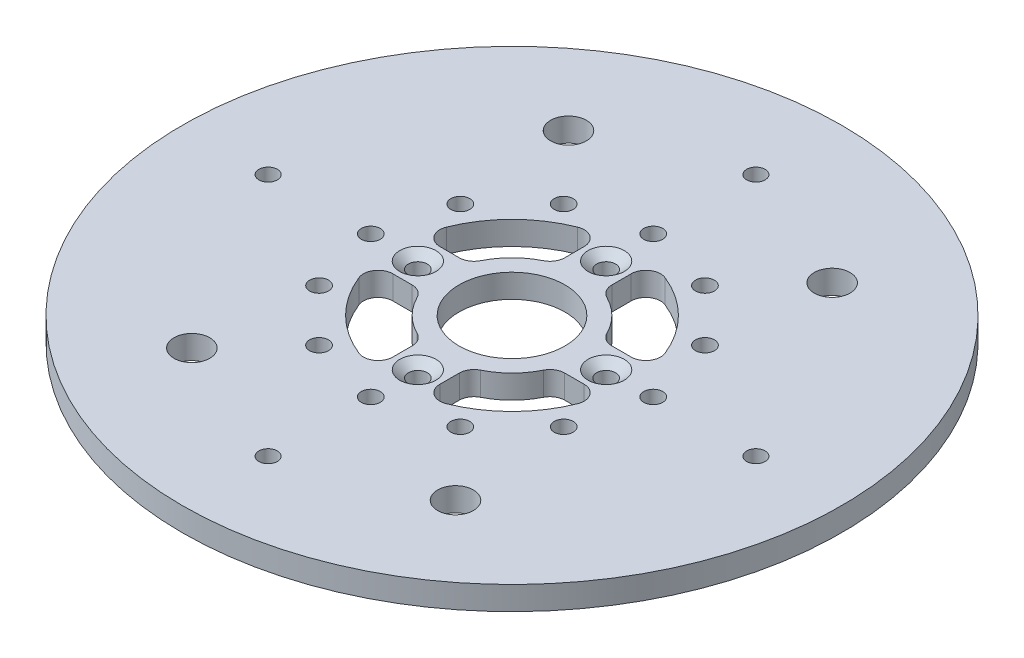
SolidWorks part; units mm, degrees
material "6061-T6 (SS)"
ref_plane "Front Plane" through (0, 0, 0) normal (0, 0, 1) x (1, 0, 0)
ref_plane "Top Plane" through (0, 0, 0) normal (0, 1, 0) x (1, 0, 0)
ref_plane "Right Plane" through (0, 0, 0) normal (1, 0, 0) x (0, 0, -1)
sketch "Sketch1" plane through (0, 0, 0) normal (0, 1, 0) x (1, 0, 0)
  circle A5 centre (0, 0) radius 88.9
  point P14 (0, 0)
  dimension "D4" = 177.8
extrude "Boss-Extrude1" add sketch "Sketch1" along normal blind 6.35
sketch "Sketch2" plane through (0, 6.35, 0) normal (0, 1, 0) x (1, 0, 0)
  circle A0 centre (0, 0) radius 14.2875
  dimension "D1" = 28.575
extrude "Cut-Extrude1" cut sketch "Sketch2" against normal through all
hole_wizard "CSK for #10 Flat Head Machine Screw (100)1" positions "Sketch5" profile "Sketch6" countersink size "#10" standard "ANSI Inch" end condition through all
sketch "Sketch5" plane through (0, 6.35, 0) normal (0, 1, 0) x (1, 0, 0)
  line L0 (0, 25.4) -> (0, 0) construction
  circle A0 centre (0, 0) radius 25.4
  point P0 (0, 25.4)
  point P13 (25.4, 0)
  point P15 (0, -25.4)
  point P17 (-25.4, 0)
  dimension "D1" = 50.8
sketch "Sketch6" plane through (0, 6.35, -25.4) normal (1, 0, 0) x (0, 0, 1)
  line L0 (0, 0) -> (0, 6.35)
  line L1 (0, 6.35) -> (2.5527, 6.35)
  line L2 (2.5527, 6.35) -> (2.5527, 1.9608)
  line L3 (2.5527, 1.9608) -> (4.8895, 0)
  line L5 (4.8895, 0) -> (0, 0)
  line L6 (-2.5527, 1.9608) -> (-4.8895, 0) construction
  line L11 (0, -6.35) -> (0, 107.95) construction
  dimension "Thru Hole Dia." = 5.1054
  dimension "Thru Hole Depth" = 6.35
  dimension "Near C'Sink Dia." = 9.779
  dimension "Near C'Sink Angle" = 100
hole_wizard "#9 (0.196) Diameter Hole1" positions "Sketch11" profile "Sketch10" hole size "#9" standard "ANSI Inch" end condition through all
sketch "Sketch11" plane through (0, 6.35, 0) normal (0, 1, 0) x (1, 0, 0)
  circle A0 centre (0, 0) radius 65.786
  point P0 (0, 65.786)
  point P9 (65.786, 0)
  point P11 (0, -65.786)
  point P13 (-65.786, 0)
  dimension "D1" = 131.572
sketch "Sketch10" plane through (0, 6.35, -65.786) normal (1, 0, 0) x (0, 0, 1)
  line L0 (0, 0) -> (0, 6.35)
  line L1 (0, 6.35) -> (2.4892, 6.35)
  line L2 (2.4892, 6.35) -> (2.4892, 0)
  line L5 (2.4892, 0) -> (0, 0)
  line L11 (0, -6.35) -> (0, 107.95) construction
  dimension "Thru Hole Dia." = 4.9784
  dimension "Thru Hole Depth" = 6.35
sketch "Sketch12" plane through (0, 6.35, 0) normal (0, 1, 0) x (1, 0, 0)
  line L0 (6.35, 48.93) -> (6.35, 79.5019)
  line L1 (48.93, 6.35) -> (79.5019, 6.35)
  line L2 (6.35, -48.93) -> (6.35, -79.5019)
  line L3 (48.93, -6.35) -> (79.5019, -6.35)
  line L4 (-48.93, -6.35) -> (-79.5019, -6.35)
  line L5 (-6.35, -48.93) -> (-6.35, -79.5019)
  line L6 (-6.35, 48.93) -> (-6.35, 79.5019)
  line L7 (-48.93, 6.35) -> (-79.5019, 6.35)
  arc A0 (9.4998, 45.0467) -> (45.0467, 9.4998) centre (0, 0) cw
  circle A1 centre (65.786, 0) radius 2.4892 construction
  circle A2 centre (0, 25.4) radius 2.5527 construction
  circle A3 centre (0, 0) radius 14.2875 construction
  arc A4 (10.8296, 83.4376) -> (83.4376, 10.8296) centre (0, 0) cw
  circle A5 centre (0, 0) radius 88.9 construction
  arc A6 (79.5019, 6.35) -> (83.4376, 10.8296) centre (79.5019, 10.3187) ccw
  arc A7 (45.0467, 9.4998) -> (48.93, 6.35) centre (48.93, 10.3187) ccw
  arc A8 (6.35, 48.93) -> (9.4998, 45.0467) centre (10.3188, 48.93) ccw
  arc A9 (6.35, 79.5019) -> (10.8296, 83.4376) centre (10.3187, 79.5019) cw
  arc A10 (9.4998, -45.0467) -> (6.35, -48.93) centre (10.3188, -48.93) ccw
  arc A11 (6.35, -79.5019) -> (10.8296, -83.4376) centre (10.3188, -79.5019) ccw
  arc A12 (83.4376, -10.8296) -> (10.8296, -83.4376) centre (0, 0) cw
  arc A13 (79.5019, -6.35) -> (83.4376, -10.8296) centre (79.5019, -10.3188) cw
  arc A14 (48.93, -6.35) -> (45.0467, -9.4998) centre (48.93, -10.3188) ccw
  arc A15 (45.0467, -9.4998) -> (9.4998, -45.0467) centre (0, 0) cw
  arc A16 (-45.0467, -9.4998) -> (-48.93, -6.35) centre (-48.93, -10.3187) ccw
  arc A17 (-79.5019, -6.35) -> (-83.4376, -10.8296) centre (-79.5019, -10.3188) ccw
  arc A18 (-10.8296, -83.4376) -> (-83.4376, -10.8296) centre (0, 0) cw
  arc A19 (-6.35, -79.5019) -> (-10.8296, -83.4376) centre (-10.3187, -79.5019) cw
  arc A20 (-6.35, -48.93) -> (-9.4998, -45.0467) centre (-10.3187, -48.93) ccw
  arc A21 (-9.4998, -45.0467) -> (-45.0467, -9.4998) centre (0, 0) cw
  arc A22 (-9.4998, 45.0467) -> (-6.35, 48.93) centre (-10.3188, 48.93) ccw
  arc A23 (-6.35, 79.5019) -> (-10.8296, 83.4376) centre (-10.3188, 79.5019) ccw
  arc A24 (-83.4376, 10.8296) -> (-10.8296, 83.4376) centre (0, 0) cw
  arc A25 (-79.5019, 6.35) -> (-83.4376, 10.8296) centre (-79.5019, 10.3188) cw
  arc A26 (-48.93, 6.35) -> (-45.0467, 9.4998) centre (-48.93, 10.3188) ccw
  arc A27 (-45.0467, 9.4998) -> (-9.4998, 45.0467) centre (0, 0) cw
  point P61 (0, 0)
  dimension "D1" = 6.35
  dimension "D3" = 31.75
  dimension "D4" = 4.7625
  dimension "D5" = 3.9688
  dimension "D2" = 6.35
  dimension "D6" = 4
extrude "Cut-Extrude2" [suppressed] cut sketch "Sketch12" against normal through all
hole_wizard "1/4-20 Tapped Hole1" positions "Sketch14" profile "Sketch15" tap size "1/4-20" standard "ANSI Inch" end condition through all
sketch "Sketch14" plane through (0, 6.35, 0) normal (0, 1, 0) x (1, 0, 0)
  line L0 (0, 0) -> (0, 38.1) construction
  line L1 (0, 0) -> (38.1, 0) construction
  circle A0 centre (0, 0) radius 38.1 construction
  point P0 (0, 38.1)
  point P12 (19.05, 32.9956)
  point P13 (32.9956, 19.05)
  point P14 (38.1, 0)
  point P15 (32.9956, -19.05)
  point P16 (19.05, -32.9956)
  point P17 (0, -38.1)
  point P18 (-19.05, -32.9956)
  point P19 (-32.9956, -19.05)
  point P20 (-38.1, 0)
  point P21 (-32.9956, 19.05)
  point P22 (-19.05, 32.9956)
  dimension "D1" = 38.1
  dimension "D2" = 12
sketch "Sketch15" plane through (0, 6.35, -38.1) normal (1, 0, 0) x (0, 0, 1)
  line L0 (0, 0) -> (0, 6.35)
  line L1 (0, 6.35) -> (2.5527, 6.35)
  line L2 (2.5527, 6.35) -> (2.5527, 0)
  line L5 (2.5527, 0) -> (0, 0)
  line L11 (0, -6.35) -> (0, 107.95) construction
  dimension "Thru Tap Drill Dia." = 5.1054
  dimension "Thru Tap Drill Depth" = 6.35
cosmetic thread "Hole Thread1" parameters "D2"=6.35
cosmetic thread "Hole Thread2" parameters "D2"=6.35
cosmetic thread "Hole Thread3" parameters "D2"=6.35
cosmetic thread "Hole Thread4" parameters "D2"=6.35
cosmetic thread "Hole Thread5" parameters "D2"=6.35
cosmetic thread "Hole Thread6" parameters "D2"=6.35
cosmetic thread "Hole Thread7" parameters "D2"=6.35
cosmetic thread "Hole Thread8" parameters "D2"=6.35
cosmetic thread "Hole Thread9" parameters "D2"=6.35
cosmetic thread "Hole Thread10" parameters "D2"=6.35
cosmetic thread "Hole Thread11" parameters "D2"=6.35
cosmetic thread "Hole Thread12" parameters "D2"=6.35
sketch "Sketch16" plane through (0, 6.35, 0) normal (0, 1, 0) x (1, 0, 0)
  line L0 (20.5764, 6.35) -> (25.7938, 6.35)
  line L1 (6.35, 20.5764) -> (6.35, 25.7938)
  line L2 (6.35, -20.5764) -> (6.35, -25.7938)
  line L3 (20.5764, -6.35) -> (25.7938, -6.35)
  line L4 (-20.5764, -6.35) -> (-25.7938, -6.35)
  line L5 (-6.35, -20.5764) -> (-6.35, -25.7938)
  line L6 (-6.35, 20.5764) -> (-6.35, 25.7938)
  line L7 (-20.5764, 6.35) -> (-25.7938, 6.35)
  arc A0 (8.5397, 17.0287) -> (17.0287, 8.5397) centre (0, 0) cw
  arc A1 (11.7929, 29.4787) -> (29.4787, 11.7929) centre (0, 0) cw
  circle A3 centre (0, 25.4) radius 2.5527 construction
  circle A4 centre (25.4, 0) radius 2.5527 construction
  circle A5 centre (0, 0) radius 14.2875 construction
  arc A6 (29.4787, 11.7929) -> (25.7938, 6.35) centre (25.7938, 10.3187) cw
  arc A7 (17.0287, 8.5397) -> (20.5764, 6.35) centre (20.5764, 10.3187) ccw
  arc A8 (8.5397, 17.0287) -> (6.35, 20.5764) centre (10.3187, 20.5764) cw
  arc A9 (6.35, 25.7938) -> (11.7929, 29.4787) centre (10.3187, 25.7938) cw
  arc A10 (8.5397, -17.0287) -> (6.35, -20.5764) centre (10.3187, -20.5764) ccw
  arc A11 (11.7929, -29.4787) -> (6.35, -25.7938) centre (10.3187, -25.7938) cw
  arc A12 (29.4787, -11.7929) -> (11.7929, -29.4787) centre (0, 0) cw
  arc A13 (25.7938, -6.35) -> (29.4787, -11.7929) centre (25.7938, -10.3188) cw
  arc A14 (17.0287, -8.5397) -> (20.5764, -6.35) centre (20.5764, -10.3188) cw
  arc A15 (17.0287, -8.5397) -> (8.5397, -17.0287) centre (0, 0) cw
  arc A16 (-17.0287, -8.5397) -> (-20.5764, -6.35) centre (-20.5764, -10.3187) ccw
  arc A17 (-29.4787, -11.7929) -> (-25.7938, -6.35) centre (-25.7938, -10.3187) cw
  arc A18 (-11.7929, -29.4787) -> (-29.4787, -11.7929) centre (0, 0) cw
  arc A19 (-6.35, -25.7938) -> (-11.7929, -29.4787) centre (-10.3188, -25.7938) cw
  arc A20 (-8.5397, -17.0287) -> (-6.35, -20.5764) centre (-10.3188, -20.5764) cw
  arc A21 (-8.5397, -17.0287) -> (-17.0287, -8.5397) centre (0, 0) cw
  arc A22 (-8.5397, 17.0287) -> (-6.35, 20.5764) centre (-10.3187, 20.5764) ccw
  arc A23 (-11.7929, 29.4787) -> (-6.35, 25.7938) centre (-10.3187, 25.7938) cw
  arc A24 (-29.4787, 11.7929) -> (-11.7929, 29.4787) centre (0, 0) cw
  arc A25 (-25.7938, 6.35) -> (-29.4787, 11.7929) centre (-25.7938, 10.3188) cw
  arc A26 (-17.0287, 8.5397) -> (-20.5764, 6.35) centre (-20.5764, 10.3188) cw
  arc A27 (-17.0287, 8.5397) -> (-8.5397, 17.0287) centre (0, 0) cw
  point P59 (0, 0)
  dimension "D1" = 31.75
  dimension "D4" = 4.7625
  dimension "D5" = 3.9688
  dimension "D2" = 6.35
  dimension "D3" = 6.35
  dimension "D6" = 4
extrude "Cut-Extrude3" cut sketch "Sketch16" against normal blind 6.35
sketch "Sketch17" plane through (0, 6.35, 0) normal (0, 1, 0) x (1, 0, 0)
  line L0 (0, 88.9) -> (0, -88.9) construction
  circle A0 centre (-35.56, -50.8) radius 4.826
  circle A1 centre (-35.56, 50.8) radius 4.826
  circle A2 centre (0, 0) radius 88.9 construction
  circle A3 centre (35.56, -50.8) radius 4.826
  circle A4 centre (35.56, 50.8) radius 4.826
  dimension "D3" = 9.652
  dimension "D6" = 9.652
  dimension "D1" = 35.56
  dimension "D2" = 50.8
  dimension "D4" = 50.8
  dimension "D5" = 35.56
extrude "Cut-Extrude4" cut sketch "Sketch17" against normal through all
